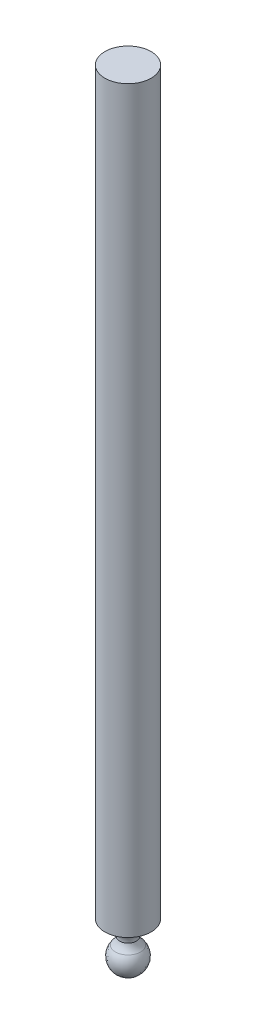
SolidWorks part; units mm, degrees
material "Простая углеродистая сталь"
ref_plane "Спереди" through (0, 0, 0) normal (0, 0, 1) x (1, 0, 0)
ref_plane "Сверху" through (0, 0, 0) normal (0, 1, 0) x (1, 0, 0)
ref_plane "Справа" through (0, 0, 0) normal (1, 0, 0) x (0, 0, -1)
sketch "Эскиз3" plane through (0, 0, 0) normal (1, 0, 0) x (0, 0, -1)
  line L0 (0, 11.108) -> (0, -11.8568) construction
  line L1 (-7.5, 0) -> (0, 0)
  line L2 (0, 0) -> (0, -15.4469)
  arc A0 (0, -15.4469) -> (-4.061, -7.3279) centre (-0.155, -10.4493) cw
  arc A1 (-2.6894, -4.9864) -> (-4.061, -7.3279) centre (-7.5844, -3.6914) cw
  arc A2 (-2.6894, -4.9864) -> (-7.5, 0) centre (-7.7337, -5.0392) ccw
revolve "Повернуть1" add sketch "Эскиз3" angle 360 about L0
sketch "Эскиз4" plane through (0, 0, 0) normal (0, 1, 0) x (1, 0, 0)
  circle A0 centre (0, 0) radius 7.5
extrude "Бобышка-Вытянуть1" add sketch "Эскиз4" along normal blind 240
